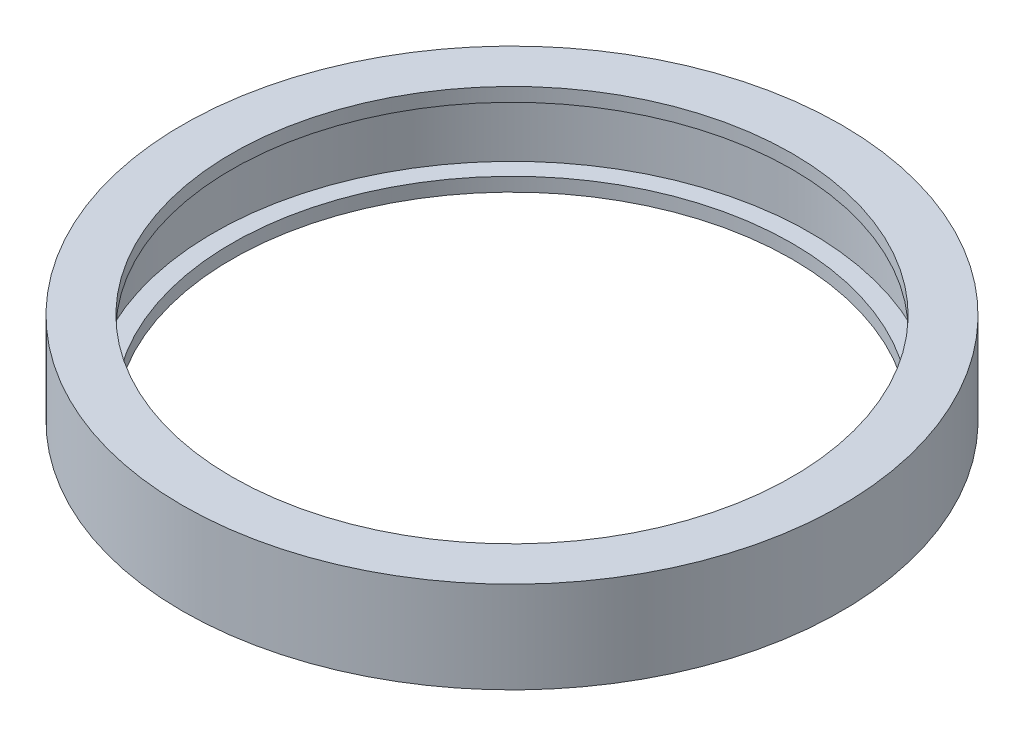
SolidWorks part; units mm, degrees
ref_plane "Front Plane" through (0, 0, 0) normal (0, 0, 1) x (1, 0, 0)
ref_plane "Top Plane" through (0, 0, 0) normal (0, 1, 0) x (1, 0, 0)
ref_plane "Right Plane" through (0, 0, 0) normal (1, 0, 0) x (0, 0, -1)
sketch "Sketch1" plane through (0, 0, 0) normal (0, 1, 0) x (1, 0, 0)
  circle A0 centre (0, 0) radius 30.6
  circle A1 centre (0, 0) radius 36
  dimension "D1" = 61.2
  dimension "D2" = 72
extrude "Boss-Extrude1" add sketch "Sketch1" along normal mid plane 10
sketch "Sketch2" plane through (0, 0, 0) normal (0, 1, 0) x (1, 0, 0)
  circle A0 centre (0, 0) radius 32.6
  dimension "D1" = 65.2
extrude "Cut-Extrude1" cut sketch "Sketch2" against normal mid plane 7
